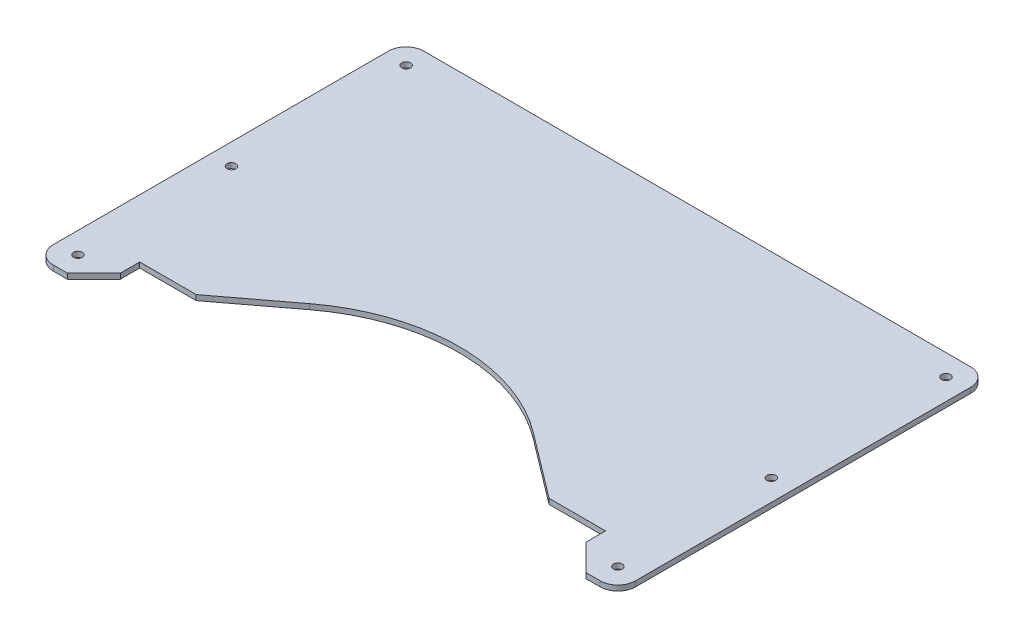
SolidWorks part; units mm, degrees
ref_plane "Face" through (0, 0, 0) normal (0, 0, 1) x (1, 0, 0)
ref_plane "Dessus" through (0, 0, 0) normal (0, 1, 0) x (1, 0, 0)
ref_plane "Droite" through (0, 0, 0) normal (1, 0, 0) x (0, 0, -1)
sketch "Esquisse1" plane through (0, 0, 0) normal (0, 1, 0) x (1, 0, 0)
  line L0 (165, 0) -> (-165, 0)
  line L1 (-165, 0) -> (-165, -210)
  line L2 (-165, -210) -> (-147, -210)
  line L3 (0, 0) -> (0, -240) construction
  line L4 (-165, -210) -> (165, -210) construction
  line L14 (165, -210) -> (147, -210)
  line L15 (165, 0) -> (165, -210)
  line L17 (-132, -184) -> (-132, -195)
  line L18 (-132, -184) -> (-100, -184)
  line L23 (-63.3633, -156.2737) -> (-100, -184)
  line L24 (-165, -159) -> (-66.9657, -159) construction
  line L25 (132, -184) -> (100, -184)
  line L26 (132, -184) -> (132, -195)
  line L27 (63.3633, -156.2737) -> (100, -184)
  line L28 (-147, -210) -> (-132, -195)
  line L36 (147, -210) -> (132, -195)
  line L38 (-148, -111) -> (-165, -111) construction
  arc A0 (-63.3633, -156.2737) -> (63.3633, -156.2737) centre (0, -240) cw
  circle A1 centre (-153, -12) radius 2.5
  circle A2 centre (153, -12) radius 2.5
  circle A3 centre (-153, -198) radius 2.5
  circle A4 centre (153, -198) radius 2.5
  circle A15 centre (-153, -111) radius 2.5
  circle A16 centre (153, -111) radius 2.5
  dimension "D3" = 32
  dimension "D9" = 5
  dimension "D10" = 105
  dimension "D13" = 5
  dimension "D25" = 15
  dimension "D27" = 21
  dimension "D29" = 5
  dimension "D1" = 165
  dimension "D2" = 210
  dimension "D4" = 99
  dimension "D11" = 12
  dimension "D12" = 12
  dimension "D14" = 12
  dimension "D15" = 12
  dimension "D21" = 26
  dimension "D22" = 25
  dimension "D23" = 45
  dimension "D28" = 30
  dimension "D30" = 12
extrude "Extrusion1" add sketch "Esquisse1" along normal blind 3
fillet "Congé1" radius 10 4 edges at (-165, 1.5, 210) (165, 1.5, 210) (165, 1.5, 0) (-165, 1.5, 0)
